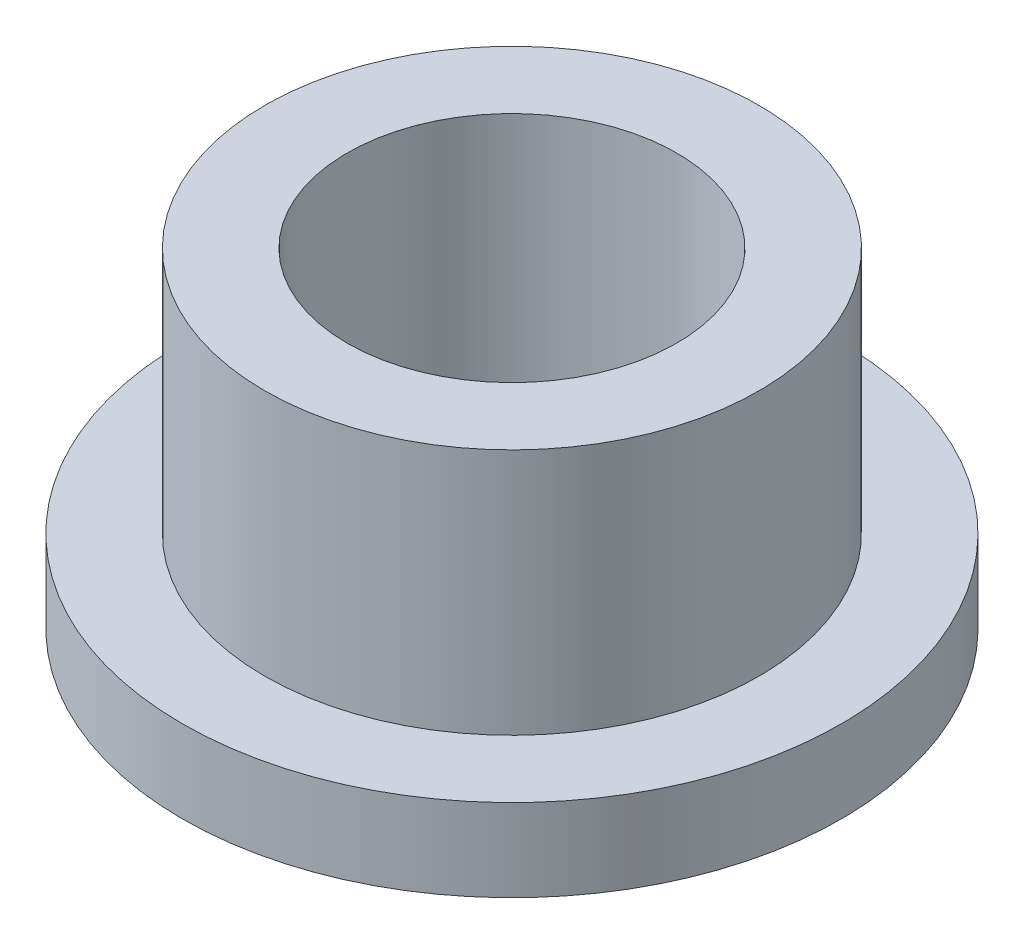
SolidWorks part; units mm, degrees
material "Commercial Bronze, UNS C22000 (90-10 Bronze)"
ref_plane "Front Plane" through (0, 0, 0) normal (0, 0, 1) x (1, 0, 0)
ref_plane "Top Plane" through (0, 0, 0) normal (0, 1, 0) x (1, 0, 0)
ref_plane "Right Plane" through (0, 0, 0) normal (1, 0, 0) x (0, 0, -1)
sketch "Sketch1" plane through (0, 0, 0) normal (0, 1, 0) x (1, 0, 0)
  circle A0 centre (0, 0) radius 6.35
  circle A1 centre (0, 0) radius 3.175
  dimension "D1" = 6.35
  dimension "D2" = 12.7
extrude "Boss-Extrude1" add sketch "Sketch1" along normal blind 1.5875
sketch "Sketch2" plane through (0, 0, 0) normal (0, 1, 0) x (1, 0, 0)
  circle A0 centre (0, 0) radius 4.7625
  circle A1 centre (0, 0) radius 3.175 construction
  circle A2 centre (0, 0) radius 3.175
  dimension "D1" = 9.525
extrude "Boss-Extrude2" add sketch "Sketch2" along normal blind 6.35
